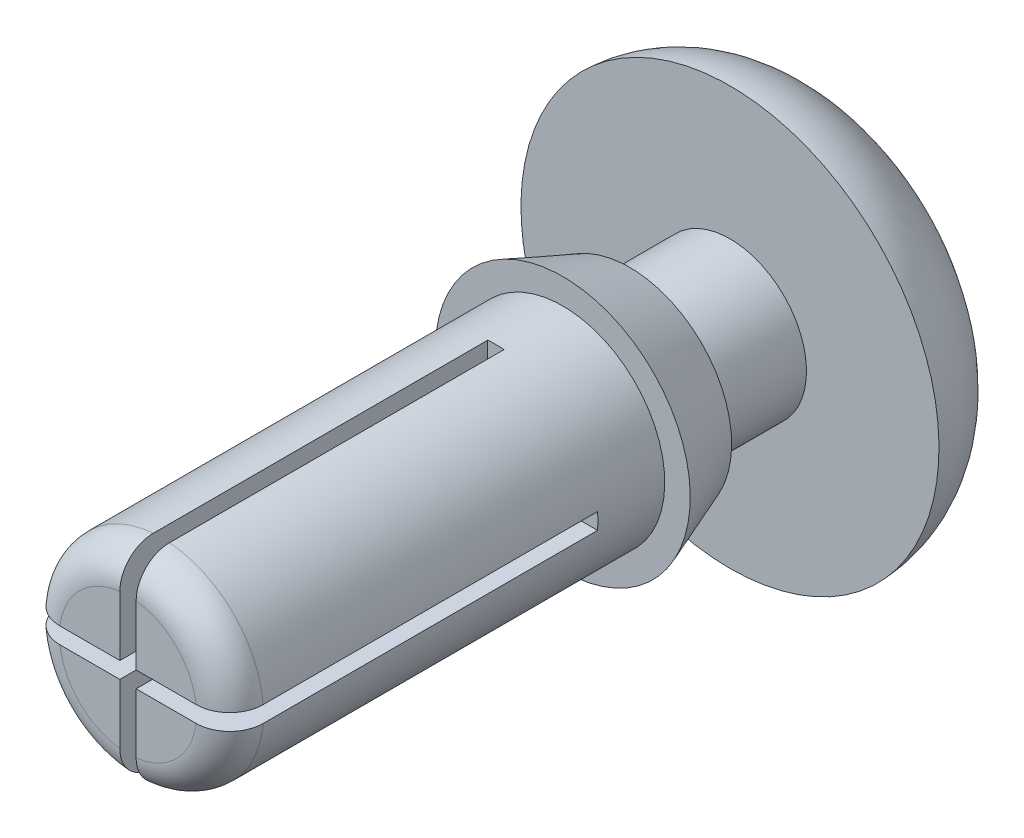
SolidWorks part; units mm, degrees
ref_plane "Front" through (0, 0, 0) normal (0, 0, 1) x (1, 0, 0)
ref_plane "Top" through (0, 0, 0) normal (0, 1, 0) x (1, 0, 0)
ref_plane "Right" through (0, 0, 0) normal (1, 0, 0) x (0, 0, -1)
sketch "layout" plane through (0, 0, 0) normal (1, 0, 0) x (0, 0, -1)
  line L0 (0, 0) -> (-6.604, 0) construction
  line L1 (0, 0) -> (1.016, 0) construction
  line L3 (2.54, 0) -> (4.064, 0) construction
  line L4 (4.064, 3.175) -> (4.064, -3.175) construction
  line L5 (1.016, 1.9367) -> (1.016, -1.9367) construction
  line L6 (0, 1.9367) -> (0, 1.5494) construction
  line L7 (2.54, 3.175) -> (2.54, -3.175) construction
  line L8 (-6.604, 1.5494) -> (-6.604, 0.7747) construction
  line L9 (-6.604, 1.5494) -> (0, 1.5494) construction
  line L10 (0, 1.9367) -> (1.016, 1.9367) construction
  line L11 (1.016, 1.162) -> (2.54, 1.1621) construction
  line L12 (2.54, 3.175) -> (4.064, 3.175) construction
  line L13 (0, -1.9367) -> (1.016, -1.9367) construction
  line L14 (2.54, -3.175) -> (4.064, -3.175) construction
  line L15 (1.016, -1.162) -> (2.54, -1.162) construction
  line L16 (1.778, -1.162) -> (1.778, 1.162) construction
  line L18 (-6.604, 0.7747) -> (-6.604, 0) construction
  line L19 (-6.604, 0) -> (-6.604, -0.7747) construction
  line L20 (-6.604, -0.7747) -> (-6.604, -1.5494) construction
  line L21 (-6.604, 1.162) -> (-6.2166, 1.162) construction
  line L22 (-6.2166, 1.162) -> (-6.2166, 1.5494) construction
  line L23 (0.508, 1.9367) -> (0.508, -1.9367) construction
  line L24 (-6.604, -1.5494) -> (0, -1.5494) construction
  line L25 (0, -1.5494) -> (0, -1.9367) construction
  dimension "D5" = 1.016
sketch "Sketch2" plane through (0, 0, 0) normal (1, 0, 0) x (0, 0, -1)
  line L0 (4.064, 0) -> (4.064, 3.175) construction
  line L1 (4.064, 3.175) -> (2.54, 3.175) construction
  line L2 (2.54, 3.175) -> (2.54, 1.1621)
  line L3 (2.54, 1.1621) -> (1.016, 1.162)
  line L4 (1.016, 1.162) -> (1.016, 1.5494)
  line L5 (1.016, 1.9367) -> (1.016, -1.9367) construction
  line L6 (1.016, 1.5494) -> (0, 1.9367)
  line L7 (0, 1.9367) -> (0, 1.5494)
  line L8 (0, 1.5494) -> (-6.604, 1.5494)
  line L9 (-6.604, 1.5494) -> (-6.604, 0)
  line L10 (-6.604, 0) -> (4.064, 0)
  line L11 (4.064, 1.5875) -> (4.064, 0)
  arc A0 (2.54, 3.175) -> (4.064, 1.5875) centre (2.4752, 1.5875) cw
revolve "Revolve1" add sketch "Sketch2" angle 360 about L10
sketch "Sketch3" plane through (0, 0, 6.604) normal (0, 0, 1) x (1, 0, 0)
  line L0 (0, 3.581) -> (0, -3.581) construction
  line L1 (-3.8098, 0) -> (3.8098, 0) construction
  line L3 (-0.124, 3.1726) -> (0.124, 3.1726)
  line L4 (-0.124, 3.1726) -> (-0.124, -3.1726)
  line L5 (-0.124, -3.1726) -> (0.124, -3.1726)
  line L6 (0.124, 3.1726) -> (0.124, -3.1726)
  line L7 (-0.124, 3.1726) -> (0.124, -3.1726) construction
  line L8 (-0.124, -3.1726) -> (0.124, 3.1726) construction
  line L9 (-3.1726, 0.124) -> (3.1726, 0.124)
  line L10 (-3.1726, 0.124) -> (-3.1726, -0.124)
  line L11 (-3.1726, -0.124) -> (3.1726, -0.124)
  line L12 (3.1726, 0.124) -> (3.1726, -0.124)
  line L13 (-3.1726, 0.124) -> (3.1726, -0.124) construction
  line L14 (-3.1726, -0.124) -> (3.1726, 0.124) construction
  circle A0 centre (0, 0) radius 3.175 construction
  point P5 (0, 0)
  point P12 (0, 0)
  dimension "D1" = 0.2479
extrude "Cut-Extrude1" cut sketch "Sketch3" against normal blind 5.588
fillet "Fillet1" radius 0.508 4 edges at (1.0956, -1.0956, 6.604) (-1.0956, -1.0956, 6.604) (-1.0956, 1.0956, 6.604) (1.0956, 1.0956, 6.604)
equation "\"D5@layout\"=\"Head Height@layout\"*(2/3)"
equation "\"D1@Sketch3\"=\"Hole Size@layout\"*.08"
equation "\"D1@Cut-Extrude1\"=\"Length@layout\"-\"D5@layout\""
